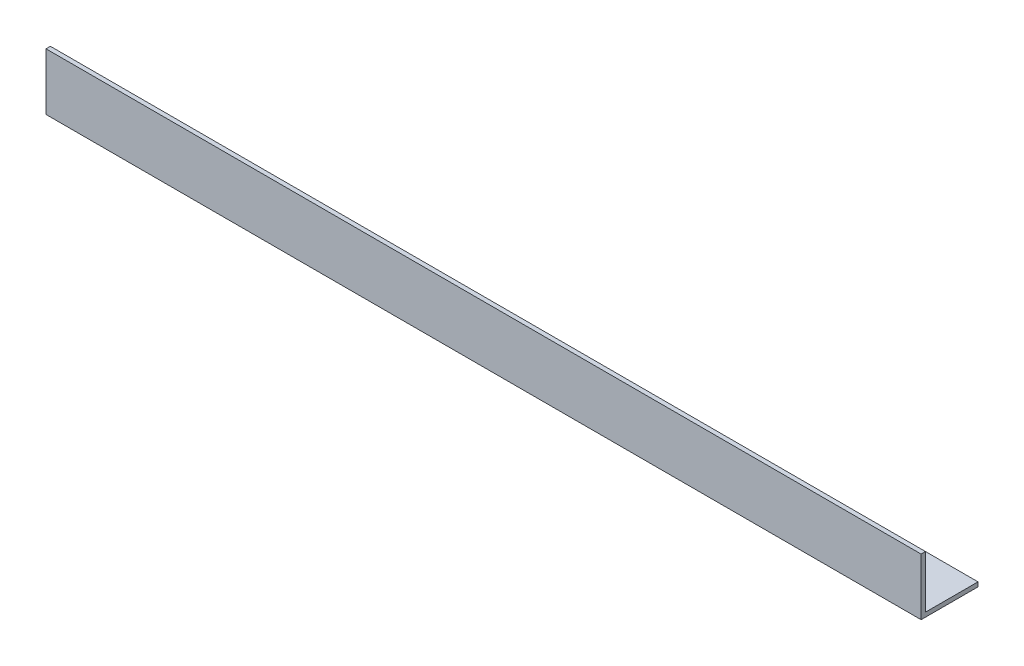
SolidWorks part; units mm, degrees
ref_plane "Спереди" through (0, 0, 0) normal (0, 0, 1) x (1, 0, 0)
ref_plane "Сверху" through (0, 0, 0) normal (0, 1, 0) x (1, 0, 0)
ref_plane "Справа" through (0, 0, 0) normal (1, 0, 0) x (0, 0, -1)
sketch "Эскиз1" plane through (0, 0, 0) normal (1, 0, 0) x (0, 0, -1)
  line L0 (0, 0) -> (0, 65)
  line L1 (0, 0) -> (65, 0)
extrude "Вытянуть-Тонкостенный1" add sketch "Эскиз1" along normal blind 1000 thin
